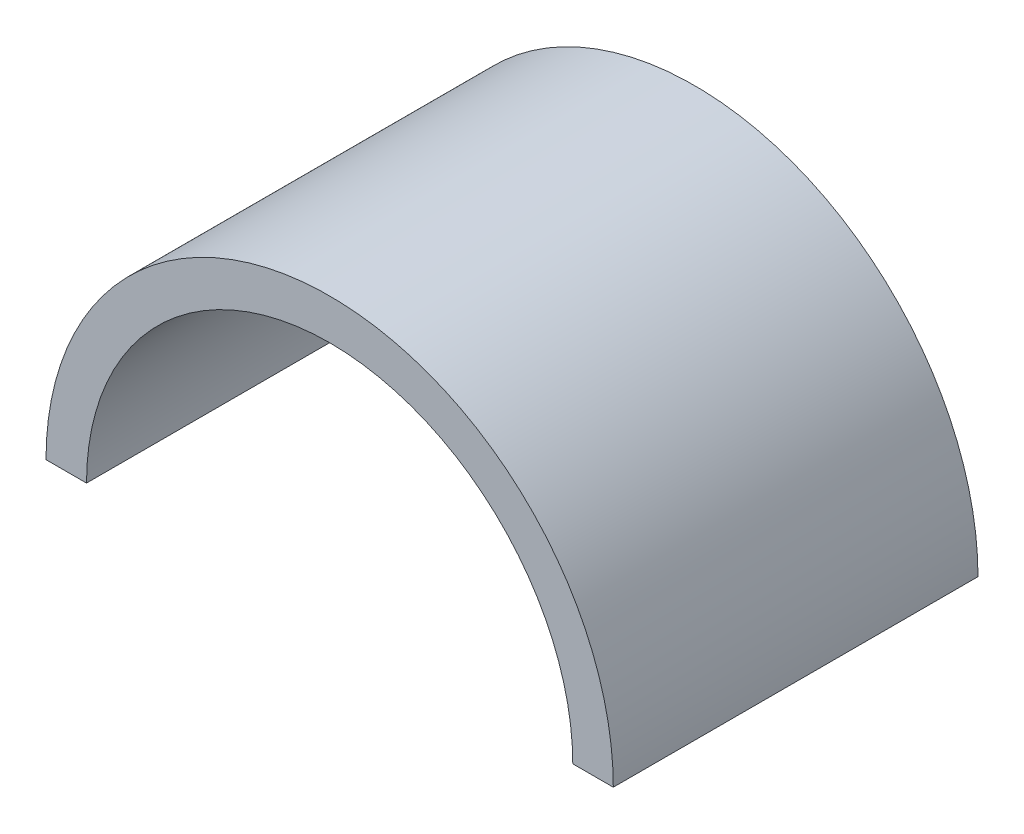
SolidWorks part; units mm, degrees
material "Aluminum Bronze"
ref_plane "Front Plane" through (0, 0, 0) normal (0, 0, 1) x (1, 0, 0)
ref_plane "Top Plane" through (0, 0, 0) normal (0, 1, 0) x (1, 0, 0)
ref_plane "Right Plane" through (0, 0, 0) normal (1, 0, 0) x (0, 0, -1)
sketch "Sketch1" plane through (0, 0, 0) normal (0, 0, 1) x (1, 0, 0)
  line L0 (7, 0) -> (-7, 0)
  circle A0 centre (0, 0) radius 6
  circle A1 centre (0, 0) radius 7
extrude "Boss-Extrude1" add sketch "Sketch1" along normal blind 9 contours L0 A1 A0
